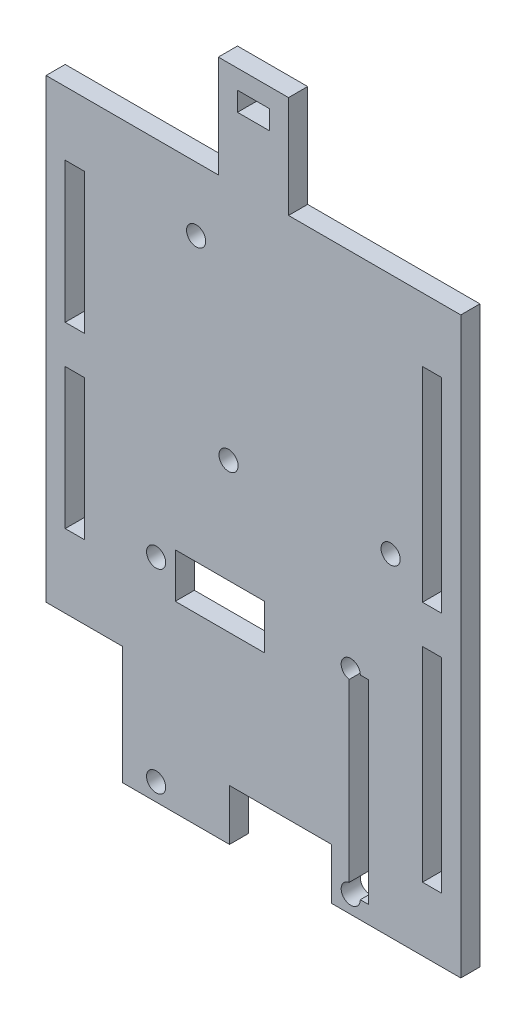
SolidWorks part; units mm, degrees
material "Custom Plastic"
ref_plane "Front Plane" through (0, 0, 0) normal (0, 0, 1) x (1, 0, 0)
ref_plane "Top Plane" through (0, 0, 0) normal (0, 1, 0) x (1, 0, 0)
ref_plane "Right Plane" through (0, 0, 0) normal (1, 0, 0) x (0, 0, -1)
sketch "Sketch1" plane through (0, 0, 0) normal (0, 0, 1) x (1, 0, 0)
  line L1 (-32.5, 45) -> (32.5, 45)
  line L2 (-32.5, 45) -> (-32.5, -45)
  line L3 (-32.5, -45) -> (32.5, -45)
  line L4 (32.5, 45) -> (32.5, -45)
  line L5 (-32.5, 45) -> (32.5, -45) construction
  line L6 (-32.5, -45) -> (32.5, 45) construction
  point P0 (0, 0)
  dimension "D1" = 65
  dimension "D2" = 90
extrude "Boss-Extrude1" add sketch "Sketch1" against normal blind 3
sketch "Sketch3" plane through (0, 0, 0) normal (0, 0, 1) x (1, 0, 0)
  line L0 (32.5, -45) -> (32.5, 45) construction
  line L3 (21.5, 7.06) -> (-3.9, 7.06) construction
  line L4 (32.5, 45) -> (-32.5, 45) construction
  circle A0 centre (-8.98, 35) radius 1.5
  circle A1 centre (-3.9, 7.06) radius 1.5
  circle A2 centre (21.5, 7.06) radius 1.5
  dimension "D5" = 3
  dimension "D6" = 3
  dimension "D7" = 3
  dimension "D1" = 27.94
  dimension "D2" = 5.08
  dimension "D3" = 25.4
  dimension "D4" = 10
  dimension "D8" = 11
extrude "Cut-Extrude2" cut sketch "Sketch3" against normal blind 3
sketch "Sketch4" plane through (0, 0, 0) normal (0, 0, 1) x (1, 0, 0)
  line L0 (-15.25, -11.75) -> (-15.25, -42.25) construction
  line L1 (-15.25, -42.25) -> (15.25, -42.25) construction
  line L2 (15.25, -42.25) -> (15.25, -11.75) construction
  circle A0 centre (-15.25, -42.25) radius 1.5
  circle A1 centre (-15.25, -11.75) radius 1.5
  circle A2 centre (15.25, -42.25) radius 1.5
  circle A3 centre (15.25, -11.75) radius 1.5
  dimension "D3" = 3
  dimension "D1" = 30.5
  dimension "D2" = 30.5
extrude "Cut-Extrude3" cut sketch "Sketch4" against normal through all
sketch "Sketch5" plane through (0, 0, 0) normal (0, 0, 1) x (1, 0, 0)
  line L0 (32.5, 45) -> (-32.5, 45) construction
  line L1 (29.5, -35) -> (26.5, -35)
  line L2 (29.5, -35) -> (29.5, -3)
  line L3 (29.5, -3) -> (26.5, -3)
  line L4 (26.5, -35) -> (26.5, -3)
  line L5 (29.5, 3) -> (26.5, 3)
  line L6 (29.5, 3) -> (29.5, 35)
  line L7 (29.5, 35) -> (26.5, 35)
  line L8 (26.5, 3) -> (26.5, 35)
  line L10 (32.5, -45) -> (32.5, 45) construction
  dimension "D1" = 6
  dimension "D2" = 32
  dimension "D3" = 10
  dimension "D4" = 3
  dimension "D5" = 3
extrude "Cut-Extrude4" cut sketch "Sketch5" against normal through all
sketch "Sketch6" plane through (0, 0, 0) normal (0, 0, 1) x (1, 0, 0)
  line L0 (-32.5, 45) -> (-32.5, -45) construction
  line L1 (-26.5, -15) -> (-29.5, -15)
  line L2 (-26.5, -15) -> (-26.5, 7)
  line L3 (-26.5, 7) -> (-29.5, 7)
  line L4 (-29.5, -15) -> (-29.5, 7)
  line L5 (-26.5, 13) -> (-29.5, 13)
  line L6 (-26.5, 13) -> (-26.5, 35)
  line L7 (-26.5, 35) -> (-29.5, 35)
  line L8 (-29.5, 13) -> (-29.5, 35)
  line L9 (-32.5, -45) -> (32.5, -45) construction
  line L10 (32.5, 45) -> (-32.5, 45) construction
  dimension "D1" = 3
  dimension "D2" = 3
  dimension "D3" = 30
  dimension "D4" = 6
  dimension "D5" = 10
extrude "Cut-Extrude5" cut sketch "Sketch6" against normal through all
sketch "Sketch7" plane through (0, 0, 0) normal (0, 0, 1) x (1, 0, 0)
  line L0 (16.75, -11.75) -> (13.75, -11.75) construction
  line L1 (18, -42.25) -> (15, -42.25)
  line L2 (18, -42.25) -> (18, -11.75)
  line L3 (18, -11.75) -> (15, -11.75)
  line L4 (15, -42.25) -> (15, -11.75)
  line L5 (16.75, -42.25) -> (13.75, -42.25) construction
  line L6 (-32.5, -45) -> (32.5, -45) construction
  line L7 (-12.25, -16.25) -> (1.75, -16.25)
  line L8 (-12.25, -16.25) -> (-12.25, -9.25)
  line L9 (-12.25, -9.25) -> (1.75, -9.25)
  line L10 (1.75, -16.25) -> (1.75, -9.25)
  line L11 (12.25, -45) -> (-3.75, -45)
  line L12 (12.25, -45) -> (12.25, -37)
  line L13 (12.25, -37) -> (-3.75, -37)
  line L14 (-3.75, -45) -> (-3.75, -37)
  circle A0 centre (15.25, -11.75) radius 1.5 construction
  circle A1 centre (15.25, -42.25) radius 1.5 construction
  circle A2 centre (-15.25, -11.75) radius 1.5 construction
  point P17 (15.25, -42.25)
  dimension "D1" = 2.5
  dimension "D2" = 3
  dimension "D3" = 7
  dimension "D4" = 14
  dimension "D5" = 3
  dimension "D6" = 3
  dimension "D7" = 2.75
  dimension "D8" = 8
  dimension "D9" = 16
extrude "Cut-Extrude6" cut sketch "Sketch7" against normal through all
sketch "Sketch8" plane through (0, 0, 0) normal (0, 0, 1) x (1, 0, 0)
  line L0 (-32.5, -45) -> (-3.75, -45) construction
  line L1 (-20.5, -45) -> (-32.5, -45)
  line L2 (-20.5, -45) -> (-20.5, -26.5)
  line L3 (-20.5, -26.5) -> (-32.5, -26.5)
  line L4 (-32.5, -45) -> (-32.5, -26.5)
  line L5 (-32.5, 45) -> (-32.5, -45) construction
  dimension "D1" = 12
  dimension "D2" = 18.5
extrude "Cut-Extrude7" cut sketch "Sketch8" against normal through all
sketch "Sketch10" plane through (0, 0, 0) normal (0, 0, 1) x (1, 0, 0)
  line L0 (0, 45) -> (0, 71) construction
  line L1 (32.5, 45) -> (-32.5, 45) construction
  line L3 (5.5, 45) -> (-5.5, 45)
  line L4 (5.5, 45) -> (5.5, 61)
  line L5 (5.5, 61) -> (-5.5, 61)
  line L6 (-5.5, 45) -> (-5.5, 61)
  line L7 (2.5, 58) -> (-2.5, 58)
  line L8 (2.5, 58) -> (2.5, 55)
  line L9 (2.5, 55) -> (-2.5, 55)
  line L10 (-2.5, 58) -> (-2.5, 55)
  point P9 (0, 61)
  point P14 (0, 58)
  dimension "D1" = 11
  dimension "D2" = 16
  dimension "D3" = 3
  dimension "D4" = 5
  dimension "D5" = 3
extrude "Boss-Extrude3" add sketch "Sketch10" against normal blind 3
